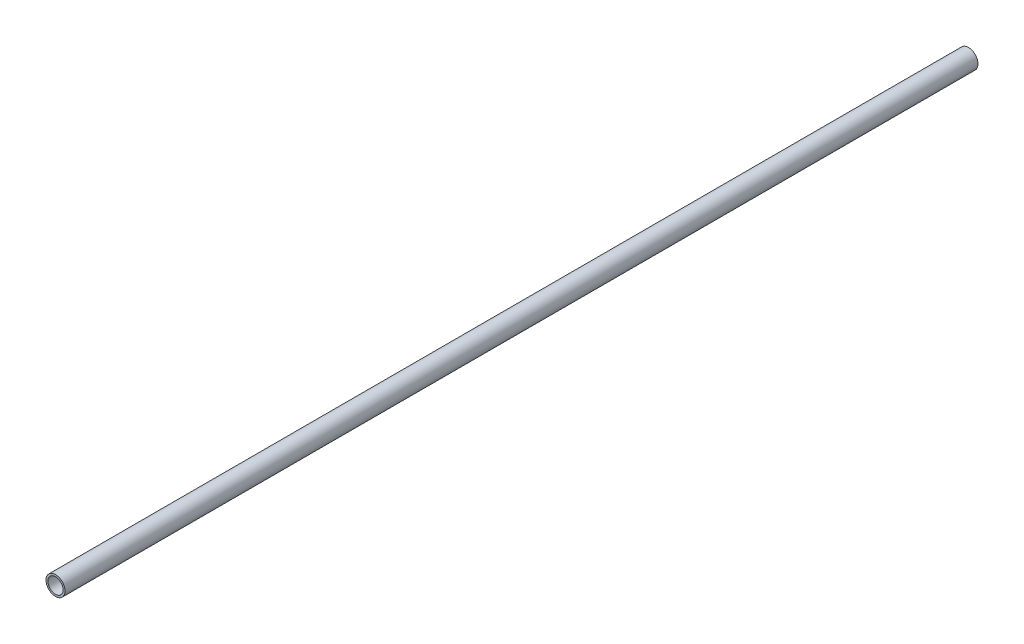
SolidWorks part; units mm, degrees
material "PVC Rigid"
ref_plane "Front Plane" through (0, 0, 0) normal (0, 0, 1) x (1, 0, 0)
ref_plane "Top Plane" through (0, 0, 0) normal (0, 1, 0) x (1, 0, 0)
ref_plane "Right Plane" through (0, 0, 0) normal (1, 0, 0) x (0, 0, -1)
sketch "Sketch1" plane through (0, 0, 0) normal (0, 0, 1) x (1, 0, 0)
  circle A0 centre (0, 0) radius 12.7
  circle A1 centre (0, 0) radius 10.16
  dimension "D1" = 25.4
  dimension "D2" = 20.32
extrude "Boss-Extrude1" add sketch "Sketch1" along normal blind 1219.2
